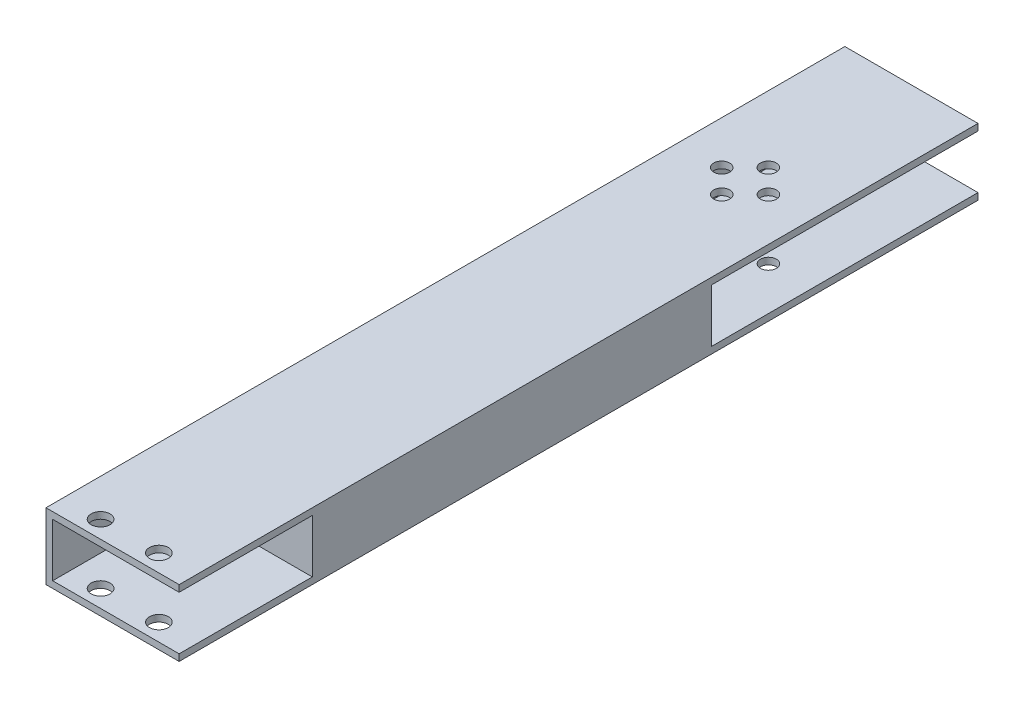
SolidWorks part; units mm, degrees
material "6061 Alloy"
ref_plane "Front Plane" through (0, 0, 0) normal (0, 0, 1) x (1, 0, 0)
ref_plane "Top Plane" through (0, 0, 0) normal (0, 1, 0) x (1, 0, 0)
ref_plane "Right Plane" through (0, 0, 0) normal (1, 0, 0) x (0, 0, -1)
sketch "Sketch1" plane through (0, 0, 0) normal (0, 0, 1) x (1, 0, 0)
  line L1 (-12.7, 6.35) -> (12.7, 6.35)
  line L2 (-12.7, 6.35) -> (-12.7, -6.35)
  line L3 (-12.7, -6.35) -> (12.7, -6.35)
  line L4 (12.7, 6.35) -> (12.7, -6.35)
  point P4 (-12.7, 0)
  point P6 (0, 6.35)
  dimension "D1" = 12.7
  dimension "D2" = 25.4
extrude "Boss-Extrude1" add sketch "Sketch1" along normal blind 127
sketch "Sketch4" plane through (0, 0, 0) normal (0, 0, -1) x (-1, 0, 0)
  line L0 (-12.7, -6.35) -> (-12.7, 6.35) construction
  line L1 (-11.43, 5.08) -> (11.43, 5.08)
  line L2 (-11.43, 5.08) -> (-11.43, -5.08)
  line L3 (-11.43, -5.08) -> (11.43, -5.08)
  line L4 (11.43, 5.08) -> (11.43, -5.08)
  line L5 (-12.7, 6.35) -> (12.7, 6.35) construction
  line L6 (12.7, -6.35) -> (-12.7, -6.35) construction
  line L7 (12.7, 6.35) -> (12.7, -6.35) construction
  dimension "D1" = 1.27
  dimension "D2" = 1.27
  dimension "D3" = 1.27
  dimension "D4" = 1.27
extrude "Cut-Extrude1" cut sketch "Sketch4" against normal through all
sketch "Sketch5" plane through (0, 6.35, 0) normal (0, 1, 0) x (1, 0, 0)
  line L2 (12.7, -127) -> (-12.7, -127) construction
  line L3 (-12.7, -127) -> (-12.7, 0) construction
  circle A0 centre (-5.588, -123.698) radius 1.8034
  circle A1 centre (5.5372, -123.698) radius 1.8034
  dimension "D1" = 3.6068
  dimension "D2" = 3.6068
  dimension "D3" = 11.1252
  dimension "D4" = 7.112
  dimension "D5" = 3.302
  dimension "D6" = 3.302
extrude "Cut-Extrude2" cut sketch "Sketch5" against normal through all both and the other way through all
sketch "Sketch6" plane through (0, -6.35, 0) normal (0, -1, 0) x (-1, 0, 0)
  line L0 (12.7, 0) -> (-12.7, 0) construction
  line L1 (12.7, -127) -> (12.7, 0) construction
  line L2 (12.7, -127) -> (-12.7, -127) construction
  circle A0 centre (4.445, -6.35) radius 1.524
  circle A1 centre (-4.4704, -6.35) radius 1.524
  circle A2 centre (0, -6.35) radius 4.445 construction
  circle A3 centre (0, -1.905) radius 1.524
  circle A4 centre (0, -10.795) radius 1.524
  dimension "D1" = 3.048
  dimension "D2" = 3.048
  dimension "D6" = 8.89
  dimension "D7" = 3.048
  dimension "D8" = 3.048
  dimension "D3" = 8.9154
  dimension "D4" = 6.35
  dimension "D5" = 8.255
  dimension "D9" = 116.205
  dimension "D10" = 120.65
extrude "Cut-Extrude3" cut sketch "Sketch6" against normal through all both contours A3 | A1 | A4 | A0
sketch "Sketch7" plane through (0, 0, 0) normal (0, 0, -1) x (-1, 0, 0)
  line L1 (-12.7, 6.35) -> (12.7, 6.35)
  line L2 (-12.7, 6.35) -> (-12.7, -6.35)
  line L3 (-12.7, -6.35) -> (12.7, -6.35)
  line L4 (12.7, 6.35) -> (12.7, -6.35)
  line L5 (-11.43, 5.08) -> (11.43, 5.08)
  line L6 (-11.43, 5.08) -> (-11.43, -5.08)
  line L7 (-11.43, -5.08) -> (11.43, -5.08)
  line L8 (11.43, 5.08) -> (11.43, -5.08)
extrude "Boss-Extrude2" add sketch "Sketch7" along normal blind 25.4
sketch "Sketch8" plane through (0, 0, -25.4) normal (0, 0, -1) x (-1, 0, 0)
  line L0 (-12.7, 6.35) -> (-12.7, -6.35) construction
  line L1 (-11.43, 5.08) -> (-12.7, 5.08)
  line L2 (-11.43, 5.08) -> (-11.43, -5.08)
  line L3 (-11.43, -5.08) -> (-12.7, -5.08)
  line L4 (-12.7, 5.08) -> (-12.7, -5.08)
  line L5 (-11.43, -5.08) -> (11.43, -5.08) construction
  dimension "D1" = 0
extrude "Cut-Extrude4" cut sketch "Sketch8" against normal up to next
sketch "Sketch9" plane through (0, 0, -25.4) normal (0, 0, -1) x (-1, 0, 0)
  line L0 (-12.7, -5.08) -> (11.43, -5.08) construction
  line L1 (11.43, 5.08) -> (-12.7, 5.08)
  line L2 (11.43, 5.08) -> (11.43, -5.08)
  line L3 (11.43, -5.08) -> (-12.7, -5.08)
  line L4 (-12.7, 5.08) -> (-12.7, -5.08)
extrude "Boss-Extrude3" add sketch "Sketch9" against normal blind 76.2 from offset 50.8
